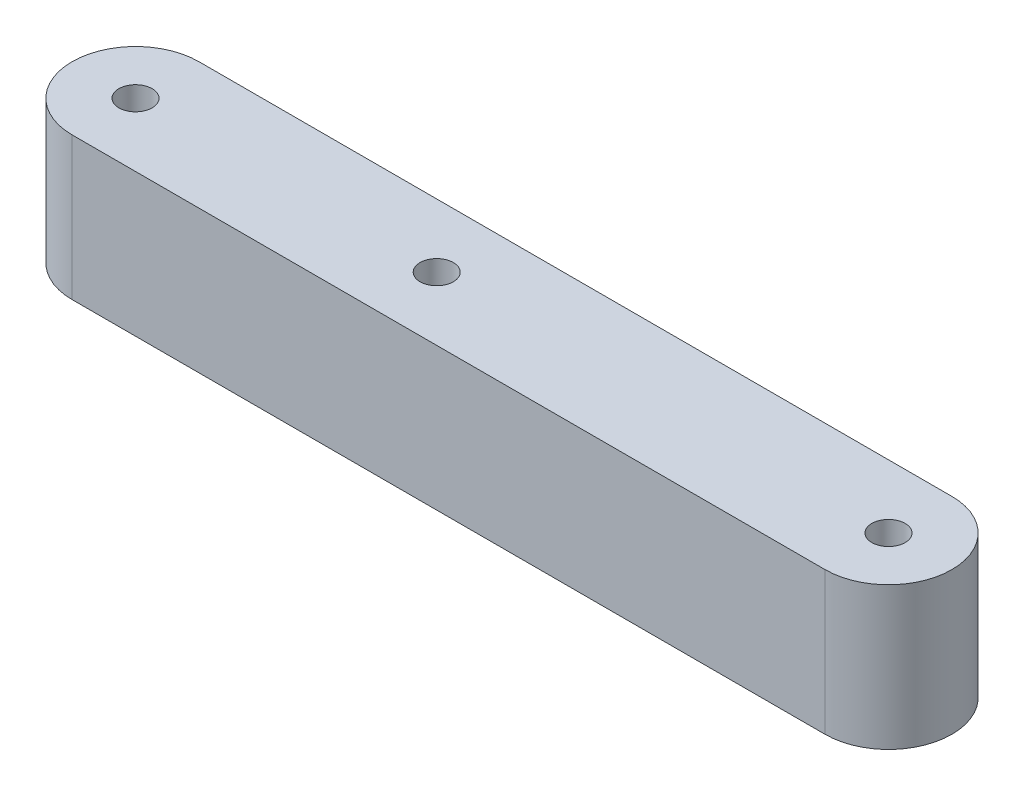
SolidWorks part; units mm, degrees
ref_plane "前视基准面" through (0, 0, 0) normal (0, 0, 1) x (1, 0, 0)
ref_plane "上视基准面" through (0, 0, 0) normal (0, 1, 0) x (1, 0, 0)
ref_plane "右视基准面" through (0, 0, 0) normal (1, 0, 0) x (0, 0, -1)
sketch "草图2" plane through (0, 0, 0) normal (0, 1, 0) x (1, 0, 0)
  line L1 (0, 0) -> (47.5, 0)
  line L3 (0, -8) -> (47.5, -8)
  arc A0 (0, 0) -> (0, -8) centre (0, -4) ccw
  arc A1 (47.5, -8) -> (47.5, 0) centre (47.5, -4) ccw
  circle A2 centre (0, -4) radius 1.05
  circle A3 centre (19, -4) radius 1.05
  circle A4 centre (47.5, -4) radius 1.05
  point P11 (0, 0)
  point P12 (0, 0)
  point P13 (47.4955, -3.1877)
  point P14 (47.4955, -3.1877)
  point P15 (49.8808, -5.3024)
  point P16 (49.8808, -5.3024)
  point P17 (49.8808, -5.3024)
  point P18 (47.4955, -3.1877)
  point P19 (0, 0)
  point P20 (45.1209, -5.3145)
  point P21 (19, -4)
  point P22 (19, -4)
  point P23 (47.5, -4)
  point P24 (47.5, -4)
  dimension "D1" = 2.1
  dimension "D2" = 2.1
  dimension "D3" = 2.1
  dimension "D7" = 4
  dimension "D8" = 4
  dimension "D4" = 19
  dimension "D6" = 28.5
extrude "凸台-拉伸1" add sketch "草图2" along normal blind 9 contours L1 A1 L3 A0
sketch "草图3" plane through (0, 0, 0) normal (0, -1, 0) x (1, 0, 0)
  circle A0 centre (0, 4) radius 1.05
  circle A1 centre (19, 4) radius 1.05
  circle A2 centre (47.5, 4) radius 1.05
  dimension "D1" = 2.1
  dimension "D2" = 2.1
  dimension "D3" = 2.1
  dimension "D4" = 28.5
  dimension "D5" = 19
extrude "切除-拉伸1" cut sketch "草图3" against normal blind 9
